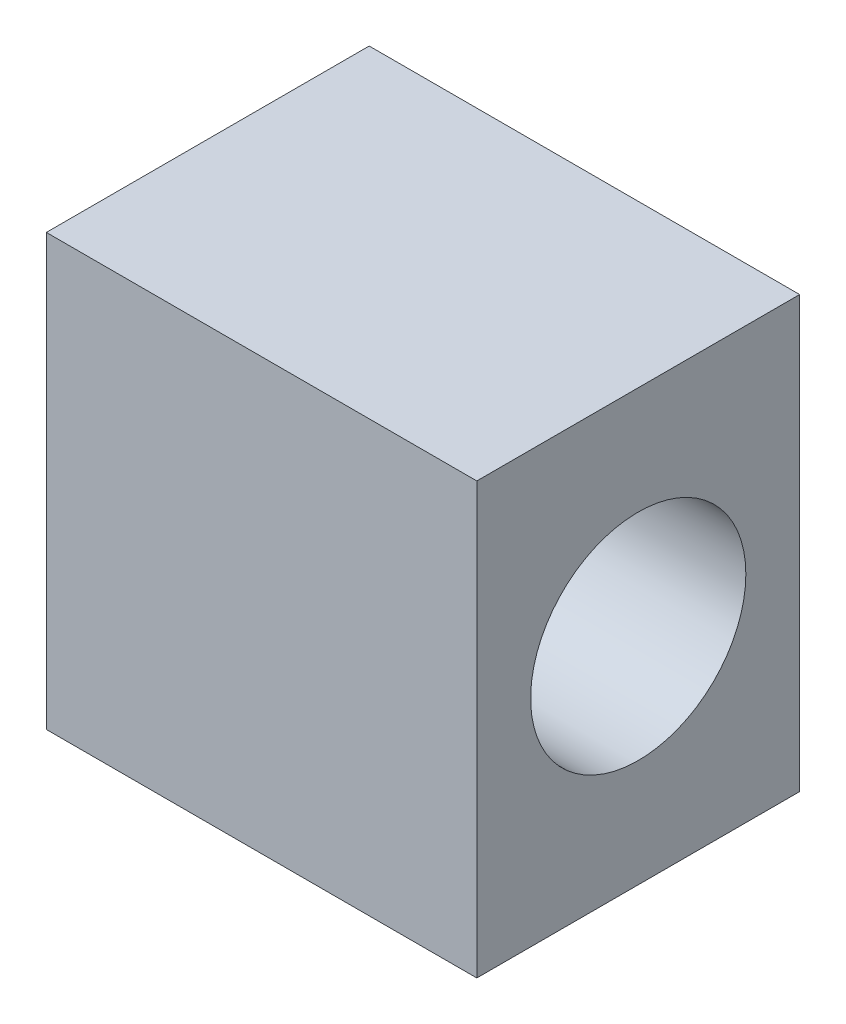
SolidWorks part; units mm, degrees
ref_plane "Front Plane" through (0, 0, 0) normal (0, 0, 1) x (1, 0, 0)
ref_plane "Top Plane" through (0, 0, 0) normal (0, 1, 0) x (1, 0, 0)
ref_plane "Right Plane" through (0, 0, 0) normal (1, 0, 0) x (0, 0, -1)
sketch "Sketch3" plane through (0, 0, 0) normal (0, 1, 0) x (1, 0, 0)
  line L0 (-10, 0) -> (10, 0) construction
  line L1 (0, 7.5) -> (0, -7.5) construction
  line L2 (-10, 7.5) -> (-10, -7.5)
  line L3 (-10, -7.5) -> (10, -7.5)
  line L4 (10, -7.5) -> (10, 7.5)
  line L5 (-10, 7.5) -> (10, 7.5)
  point P4 (0, 0)
  point P8 (0, 0)
  point P11 (-10, 0)
  point P16 (-10, 7.5)
  dimension "D1" = 15
  dimension "D2" = 20
extrude "Boss-Extrude1" add sketch "Sketch3" along normal blind 20
sketch "Sketch5" plane through (10, 0, 0) normal (1, 0, 0) x (0, 0, -1)
  circle A1 centre (0, 10) radius 5
extrude "Cut-Extrude1" cut sketch "Sketch5" against normal blind 10
sketch "Sketch6" plane through (-10, 0, 0) normal (-1, 0, 0) x (0, 0, 1)
  circle A0 centre (0, 10) radius 5
sketch "Sketch7" plane through (0, 0, 0) normal (0, -1, 0) x (1, 0, 0)
  circle A0 centre (0, 0) radius 5
extrude "Cut-Extrude2" cut sketch "Sketch6" against normal blind 4 contours A0
